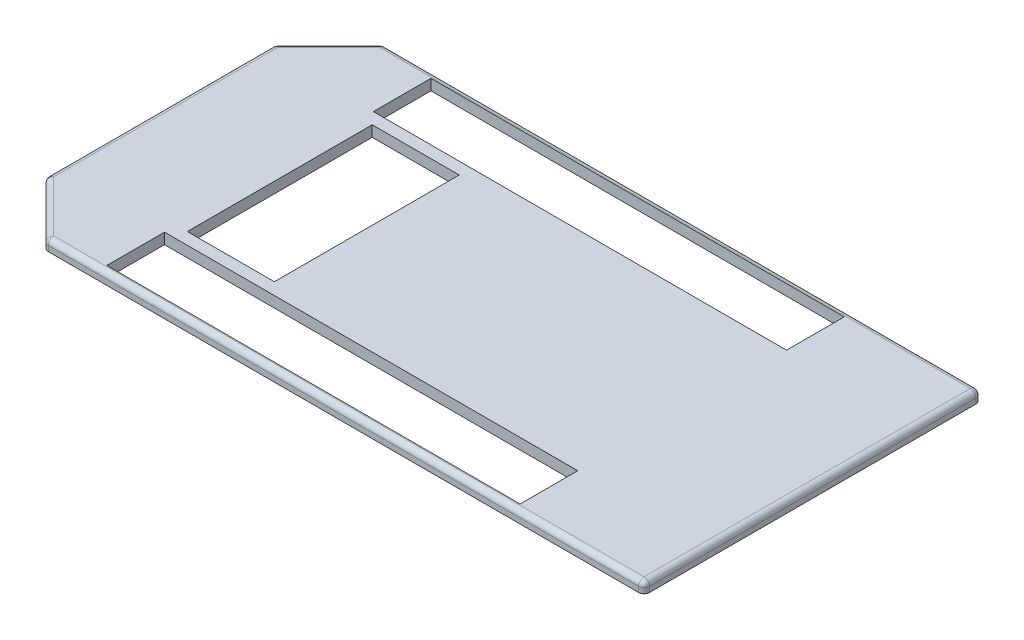
SolidWorks part; units mm, degrees
ref_plane "Front Plane" through (0, 0, 0) normal (0, 0, 1) x (1, 0, 0)
ref_plane "Top Plane" through (0, 0, 0) normal (0, 1, 0) x (1, 0, 0)
ref_plane "Right Plane" through (0, 0, 0) normal (1, 0, 0) x (0, 0, -1)
sketch "Sketch1" plane through (0, 0, 0) normal (0, 1, 0) x (1, 0, 0)
  line L0 (-300, 105) -> (-250, 155)
  line L1 (-250, 155) -> (300, 155)
  line L2 (-300, 105) -> (-300, -105)
  line L3 (-250, -155) -> (300, -155)
  line L4 (300, 155) -> (300, -155)
  line L5 (-255.799, 169) -> (314, 169) construction
  line L6 (314, 169) -> (314, -169) construction
  line L7 (-55, 0) -> (55, 0) construction
  line L8 (-300, -105) -> (-250, -155)
  line L9 (-255.799, -169) -> (314, -169) construction
  line L10 (-314, -110.799) -> (-255.799, -169) construction
  line L11 (-314, 110.799) -> (-314, -110.799) construction
  line L12 (-314, 110.799) -> (-255.799, 169) construction
  point P0 (0, 0)
  dimension "D1" = 14
  dimension "D2" = 310
  dimension "D3" = 50
  dimension "D4" = 50
extrude "Boss-Extrude2" add sketch "Sketch1" along normal blind 10
fillet "Fillet1" radius 5 12 edges at (25, 10, 155) (-275, 10, 130) (-300, 10, 0) (-275, 10, -130) (25, 10, -155) (300, 10, 0) (300, 5, -155) (-250, 5, -155) (-300, 5, -105) (-300, 5, 105) (-250, 5, 155) (300, 5, 155)
sketch "Sketch7" plane through (0, 0, 0) normal (0, -1, 0) x (1, 0, 0)
  line L0 (295, -155) -> (-247.9289, -155) construction
  line L1 (180, -149) -> (-200, -149)
  line L2 (180, -149) -> (180, -96)
  line L3 (180, -96) -> (-200, -96)
  line L4 (-200, -149) -> (-200, -96)
  line L5 (300, 150) -> (300, -150) construction
  line L6 (5.5, 0) -> (-5.5, 0) construction
  line L7 (180, 96) -> (-200, 96)
  line L8 (-200, 149) -> (-200, 96)
  line L9 (180, 149) -> (-200, 149)
  line L10 (180, 149) -> (180, 96)
  line L12 (-190, 85) -> (-110, 85)
  line L13 (-190, 85) -> (-190, -85)
  line L14 (-190, -85) -> (-110, -85)
  line L15 (-110, 85) -> (-110, -85)
  point P18 (-110, 0)
  dimension "D1" = 380
  dimension "D2" = 6
  dimension "D3" = 53
  dimension "D4" = 120
  dimension "D5" = 170
  dimension "D6" = 80
  dimension "D7" = 10
extrude "Cut-Extrude1" cut sketch "Sketch7" against normal blind 10
